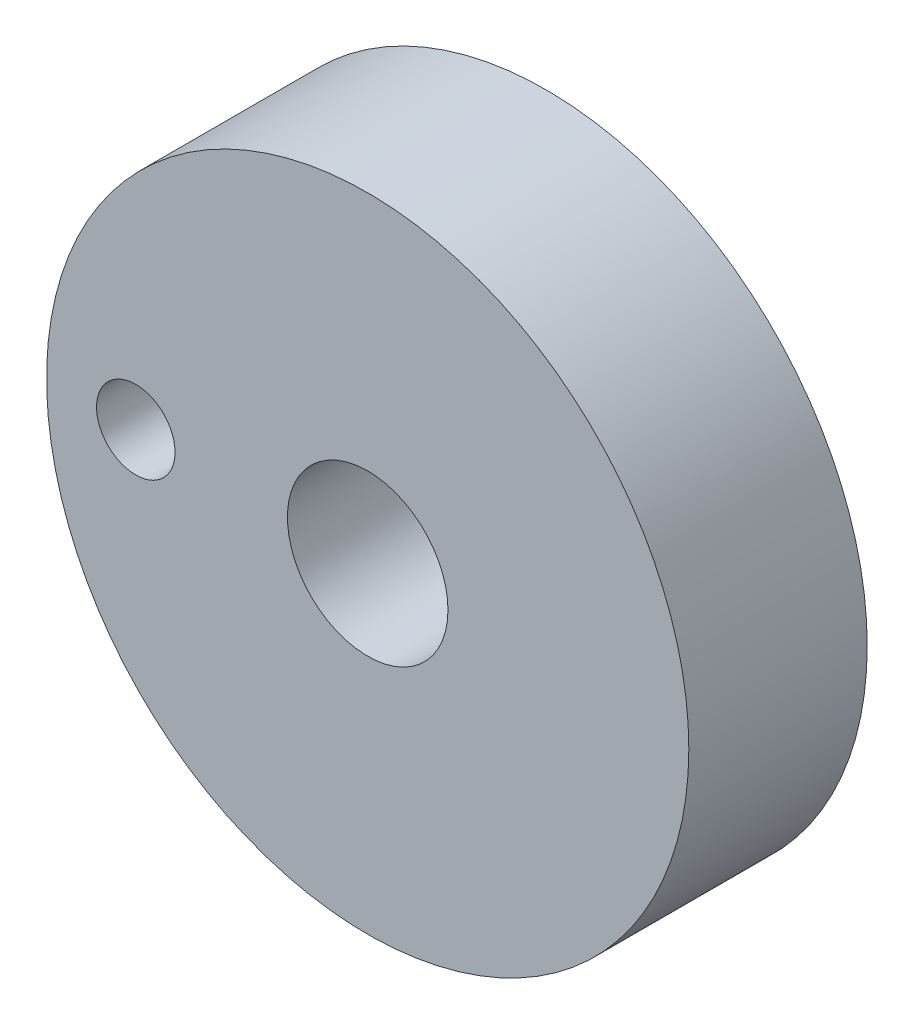
SolidWorks part; units mm, degrees
ref_plane "Front" through (0, 0, 0) normal (0, 0, 1) x (1, 0, 0)
ref_plane "Top" through (0, 0, 0) normal (0, 1, 0) x (1, 0, 0)
ref_plane "Right" through (0, 0, 0) normal (1, 0, 0) x (0, 0, -1)
sketch "Sketch1" plane through (0, 0, 0) normal (0, 0, 1) x (1, 0, 0)
  line L0 (0, 0) -> (-6.5, 0) construction
  line L1 (-6.5, 0) -> (0, 6.5) construction
  line L2 (0, 6.5) -> (0, 0) construction
  line L3 (0, 0) -> (6.5, 0) construction
  line L4 (6.5, 0) -> (0, -6.5) construction
  line L5 (0, -6.5) -> (0, 0) construction
  circle A0 centre (0, 0) radius 9
  circle A1 centre (0, 0) radius 2.25
  circle A2 centre (-6.5, 0) radius 1.1
  circle A3 centre (0, 0) radius 6.5 construction
  dimension "D1" = 18
  dimension "D2" = 4.5
  dimension "D3" = 2.2
  dimension "D4" = 13
extrude "Boss-Extrude1" add sketch "Sketch1" along normal blind 5
